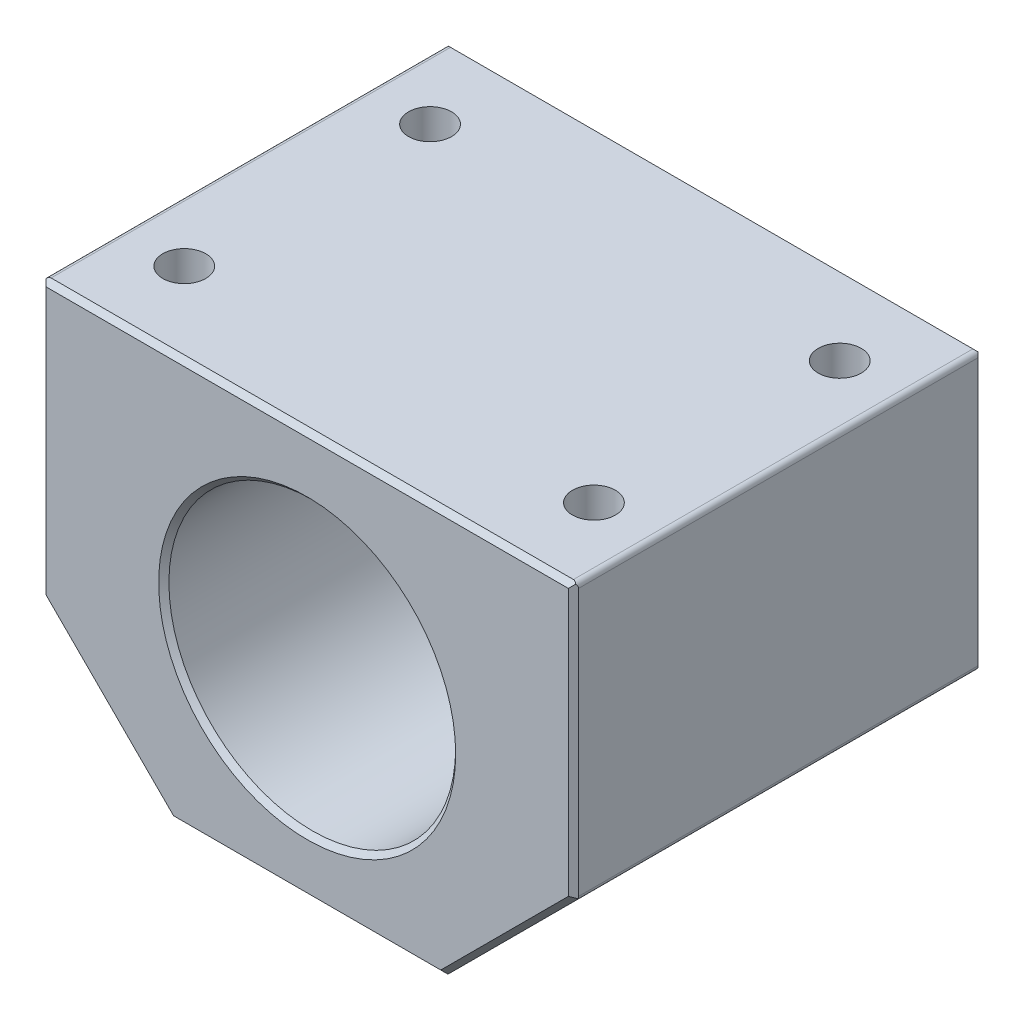
SolidWorks part; units mm, degrees
ref_plane "Front Plane" through (0, 0, 0) normal (0, 0, 1) x (1, 0, 0)
ref_plane "Top Plane" through (0, 0, 0) normal (0, 1, 0) x (1, 0, 0)
ref_plane "Right Plane" through (0, 0, 0) normal (1, 0, 0) x (0, 0, -1)
sketch "Sketch1" plane through (0, 0, 0) normal (0, 0, 1) x (1, 0, 0)
  line L0 (-13.25, -19.5) -> (13.25, -19.5)
  line L1 (13.25, -19.5) -> (26, -6.75)
  line L2 (26, -6.75) -> (26, 20)
  line L3 (26, 20) -> (-26, 20)
  line L4 (0, 20) -> (0, -19.5) construction
  line L5 (-13.25, -19.5) -> (-26, -6.75)
  line L6 (-26, -6.75) -> (-26, 20)
  circle A0 centre (0, 0) radius 14
  point P3 (0, -14)
  dimension "D5" = 28
  dimension "D1" = 39.5
  dimension "D2" = 26
  dimension "D3" = 135
  dimension "D4" = 5.5
  dimension "D6" = 13.25
extrude "Boss-Extrude1" add sketch "Sketch1" along normal mid plane 40
hole_wizard "M5x0.8 Tapped Hole1" positions "Sketch3" profile "Sketch4" tap size "M5x0.8" standard "ANSI Metric"
sketch "Sketch3" plane through (0, 0, -20) normal (0, 0, -1) x (-1, 0, 0)
  line L0 (0, 0) -> (-13.435, 13.435) construction
  line L3 (0, 0) -> (-26, 0) construction
  line L4 (-26, -6.75) -> (-26, 20) construction
  point P0 (-13.435, 13.435)
  dimension "D1" = 45
  dimension "D2" = 19
sketch "Sketch4" plane through (13.435, 13.435, -20) normal (1, 0, 0) x (0, 1, 0)
  line L0 (0, 0) -> (0, 16.9218)
  line L1 (0, 16.9218) -> (2.1, 15.66)
  line L2 (2.1, 15.66) -> (2.1, 0)
  line L5 (2.1, 0) -> (0, 0)
  line L10 (0, 16.9218) -> (-2.1, 15.66) construction
  line L11 (0, -6.35) -> (0, 107.95) construction
  dimension "Tap Drill Dia." = 4.2
  dimension "Tap Drill Depth" = 15.66
  dimension "Drill Angle" = 118
cosmetic thread "Hole Thread1" parameters "D1"=10, "D2"=5
pattern_circular "CirPattern1" count 3 every 45 about axis through (0, 0, 0) along (0, 0, 1) of "M5x0.8 Tapped Hole1"
cosmetic thread "Hole Thread2" parameters "D1"=10, "D2"=5
cosmetic thread "Hole Thread3" parameters "D1"=10, "D2"=5
mirror "Mirror1" about plane through (0, 0, 0) normal (1, 0, 0) of "CirPattern1", "M5x0.8 Tapped Hole1"
cosmetic thread "Hole Thread4" parameters "D1"=10, "D2"=5
cosmetic thread "Hole Thread5" parameters "D1"=10, "D2"=5
cosmetic thread "Hole Thread6" parameters "D1"=10, "D2"=5
hole_wizard "M5x0.8 Tapped Hole2" positions "Sketch5" profile "Sketch6" tap size "M5x0.8" standard "ANSI Metric"
sketch "Sketch5" plane through (0, 20, 0) normal (0, 1, 0) x (1, 0, 0)
  line L0 (-20, 12) -> (-20, -12) construction
  line L3 (0, 0) -> (-20, 0) construction
  point P0 (-20, 12)
  point P3 (-20, -12)
  dimension "D1" = 24
  dimension "D2" = 20
sketch "Sketch6" plane through (-20, 20, -12) normal (1, 0, 0) x (0, 0, 1)
  line L0 (0, 0) -> (0, 16.7618)
  line L1 (0, 16.7618) -> (2.1, 15.5)
  line L2 (2.1, 15.5) -> (2.1, 0)
  line L5 (2.1, 0) -> (0, 0)
  line L10 (0, 16.7618) -> (-2.1, 15.5) construction
  line L11 (0, -6.35) -> (0, 107.95) construction
  dimension "Tap Drill Dia." = 4.2
  dimension "Tap Drill Depth" = 15.5
  dimension "Drill Angle" = 118
cosmetic thread "Hole Thread7" parameters "D1"=10, "D2"=5
cosmetic thread "Hole Thread8" parameters "D1"=10, "D2"=5
mirror "Mirror2" about plane through (0, 0, 0) normal (1, 0, 0) of "M5x0.8 Tapped Hole2"
cosmetic thread "Hole Thread9" parameters "D1"=10, "D2"=5
cosmetic thread "Hole Thread10" parameters "D1"=10, "D2"=5
chamfer "Chamfer1" distance 0.5 angle 45 14 edges at (26, 6.625, 20) (19.625, -13.125, 20) (0, -19.5, 20) (-19.625, -13.125, 20) (-26, 6.625, 20) (0, 20, 20) (14, 0, 20) (14, 0, -20) (-26, 6.625, -20) (-19.625, -13.125, -20) (0, -19.5, -20) (19.625, -13.125, -20) (26, 6.625, -20) (0, 20, -20)
fillet "Fillet1" radius 0.5 6 edges at (26, 20, 0) (26, -6.75, 0) (13.25, -19.5, 0) (-13.25, -19.5, 0) (-26, -6.75, 0) (-26, 20, 0)
